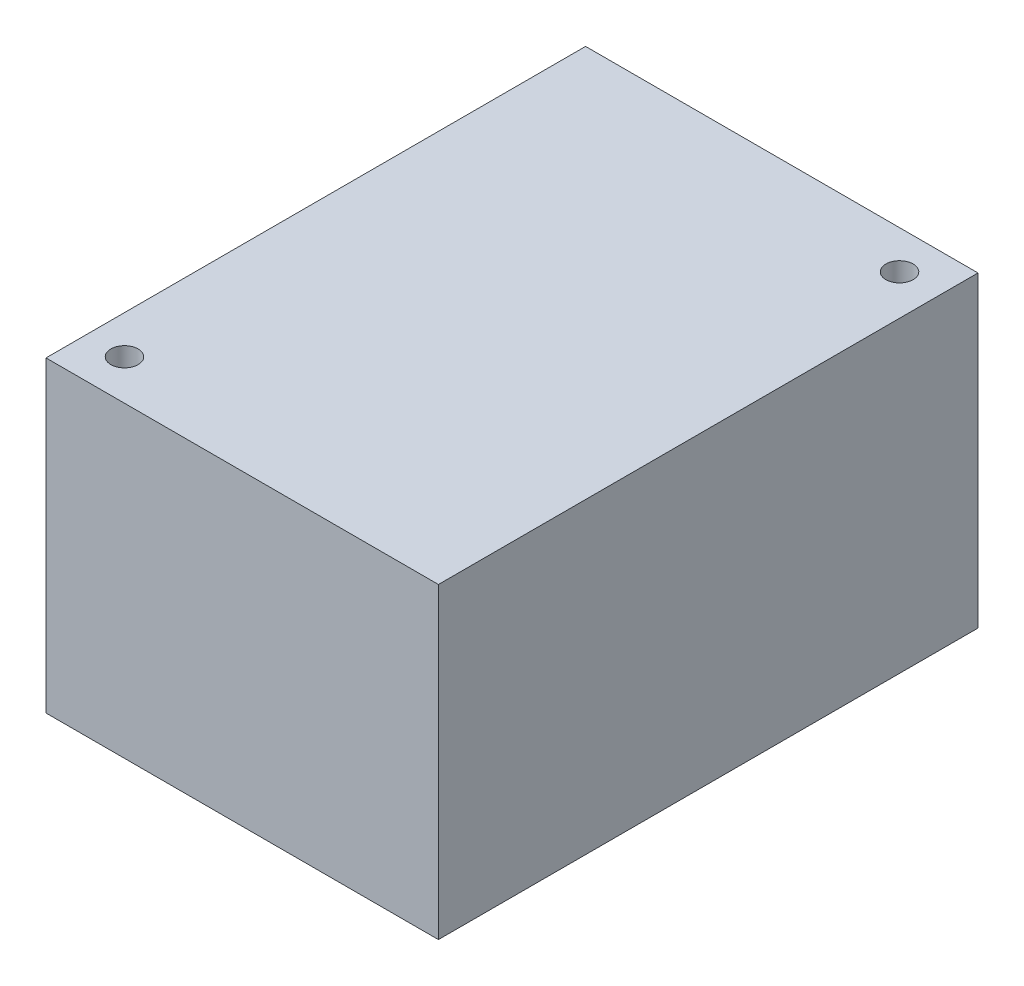
SolidWorks part; units mm, degrees
ref_plane "Front Plane" through (0, 0, 0) normal (0, 0, 1) x (1, 0, 0)
ref_plane "Top Plane" through (0, 0, 0) normal (0, 1, 0) x (1, 0, 0)
ref_plane "Right Plane" through (0, 0, 0) normal (1, 0, 0) x (0, 0, -1)
sketch "Sketch1" plane through (0, 205.7944, 0) normal (0, 1, 0) x (1, 0, 0)
  line L1 (39.9365, -182.5441) -> (79.9365, -182.5441)
  line L2 (39.9365, -182.5441) -> (39.9365, -237.5441)
  line L3 (39.9365, -237.5441) -> (79.9365, -237.5441)
  line L4 (79.9365, -182.5441) -> (79.9365, -237.5441)
  point P4 (0, 0)
extrude "Boss-Extrude1" add sketch "Sketch1" along normal up to surface (31.35 mm away) from surface at -14.3
hole_wizard "7/64 (0.10938) Diameter Hole1" positions "Sketch2" profile "Sketch3" hole size "7/64" standard "ANSI Inch" end condition through all
sketch "Sketch2" plane through (0, 191.4944, 0) normal (0, -1, 0) x (-1, 0, 0)
  arc A0 (-75.8365, -187.7941) -> (-75.8365, -185.0941) centre (-75.8365, -186.4441) ccw construction
  arc A1 (-43.8365, -234.7941) -> (-43.8365, -232.0941) centre (-43.8365, -233.4441) ccw construction
  point P0 (-75.8365, -186.4441)
  point P2 (-43.8365, -233.4441)
  point P5 (0, 0)
  point P9 (0, 0)
sketch "Sketch3" plane through (75.8365, 191.4944, 186.4441) normal (1, 0, 0) x (0, 0, -1)
  line L0 (0, 0) -> (0, 31.35)
  line L1 (0, 31.35) -> (1.3891, 31.35)
  line L2 (1.3891, 31.35) -> (1.3891, 0)
  line L5 (1.3891, 0) -> (0, 0)
  line L11 (0, -6.35) -> (0, 107.95) construction
  dimension "Thru Hole Dia." = 2.7783
  dimension "Thru Hole Depth" = 31.35
